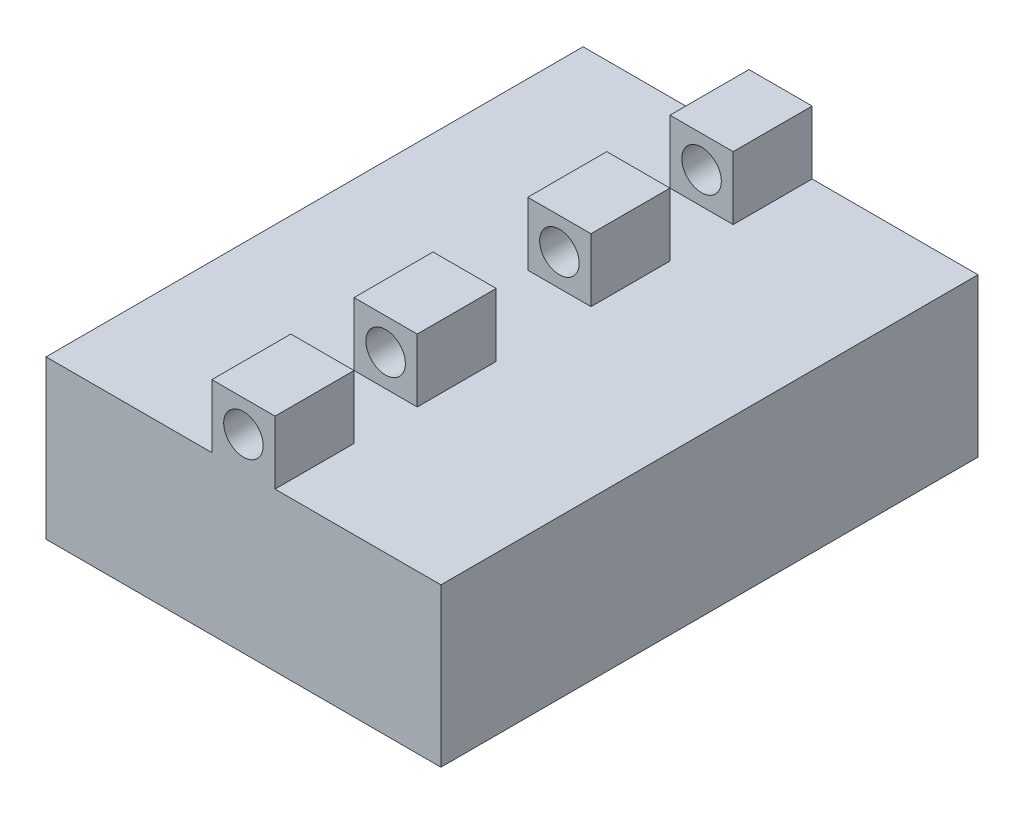
SolidWorks part; units mm, degrees
ref_plane "Front Plane" through (0, 0, 0) normal (0, 0, 1) x (1, 0, 0)
ref_plane "Top Plane" through (0, 0, 0) normal (0, 1, 0) x (1, 0, 0)
ref_plane "Right Plane" through (0, 0, 0) normal (1, 0, 0) x (0, 0, -1)
sketch "Sketch1" plane through (0, 0, 0) normal (0, 1, 0) x (1, 0, 0)
  line L1 (0, 0) -> (250, 0)
  line L2 (0, 0) -> (0, -340)
  line L3 (0, -340) -> (250, -340)
  line L4 (250, 0) -> (250, -340)
  dimension "D1" = 250
  dimension "D2" = 340
extrude "Boss-Extrude1" add sketch "Sketch1" along normal blind 100
sketch "Sketch3" plane through (0, 0, 340) normal (0, 0, 1) x (1, 0, 0)
  line L0 (0, 100) -> (0, 0) construction
  line L1 (0, 100) -> (250, 100) construction
  line L2 (105, 100) -> (145, 100)
  line L8 (105, 132.5) -> (105, 120)
  line L9 (105, 120) -> (105, 100)
  line L11 (145, 140) -> (105, 140)
  line L12 (105, 140) -> (105, 132.5)
  line L13 (145, 120) -> (145, 100)
  line L14 (145, 132.5) -> (145, 120)
  line L15 (145, 140) -> (145, 132.5)
  circle A0 centre (125, 120) radius 12.5
  point P16 (125, 140)
  dimension "D2" = 25
  dimension "D3" = 20
  dimension "D1" = 125
extrude "Boss-Extrude2" add sketch "Sketch3" against normal through all
sketch "Sketch4" plane through (0, 140, 0) normal (0, 1, 0) x (1, 0, 0)
  line L0 (145, 0) -> (145, -340) construction
  line L1 (105, -250) -> (145, -250)
  line L2 (105, -250) -> (105, -290)
  line L3 (105, -290) -> (145, -290)
  line L4 (145, -250) -> (145, -290)
  line L5 (145, -340) -> (105, -340) construction
  line L6 (250, 0) -> (145, 0) construction
  line L7 (145, 0) -> (105, 0) construction
  line L8 (105, -50) -> (145, -50)
  line L9 (145, -90) -> (145, -50)
  line L10 (105, -90) -> (105, -50)
  line L11 (105, -90) -> (145, -90)
  line L12 (105, -200) -> (145, -200)
  line L13 (105, -200) -> (105, -140)
  line L14 (105, -140) -> (145, -140)
  line L15 (145, -200) -> (145, -140)
  line L16 (105, 0) -> (105, -340) construction
  dimension "D1" = 0
  dimension "D2" = 0
  dimension "D3" = 50
  dimension "D4" = 40
  dimension "D5" = 140
  dimension "D6" = 140
  dimension "D7" = 0
  dimension "D8" = 0
  dimension "D9" = 50
  dimension "D10" = 50
extrude "Cut-Extrude1" cut sketch "Sketch4" against normal blind 40
